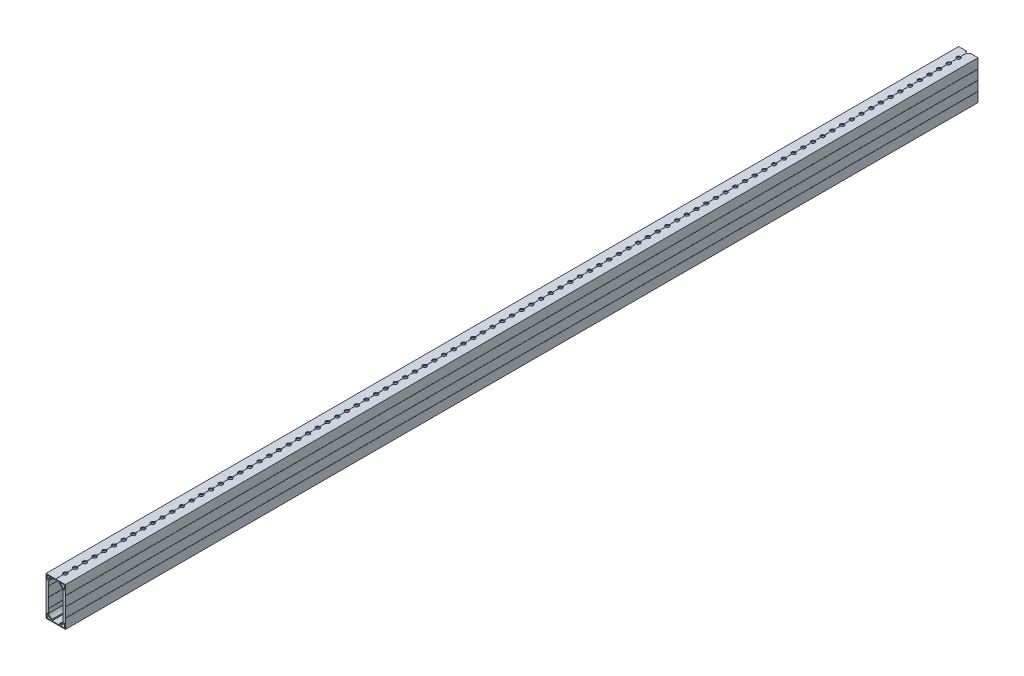
SolidWorks part; units mm, degrees
material "6061 Alloy"
ref_plane "Front Plane" through (0, 0, 0) normal (0, 0, 1) x (1, 0, 0)
ref_plane "Top Plane" through (0, 0, 0) normal (0, 1, 0) x (1, 0, 0)
ref_plane "Right Plane" through (0, 0, 0) normal (1, 0, 0) x (0, 0, -1)
other "Configuration Table"
ref_plane "Plane1" through (-12.7, 0, 0) normal (-1, 0, 0) x (0, -1, 0)
sketch "Sketch1" plane through (-12.7, 0, 0) normal (-1, 0, 0) x (0, -1, 0)
  line L0 (-25.4, -596.9) -> (25.4, -596.9)
  line L1 (25.4, -596.9) -> (25.4, 596.9)
  line L2 (25.4, 596.9) -> (-25.4, 596.9)
  line L3 (-25.4, 596.9) -> (-25.4, -596.9)
  line L4 (-25.4, -596.9) -> (25.4, 596.9) construction
  point P6 (0, 0)
  dimension "D1" = 50.8
  dimension "D2" = 1193.8
extrude "Boss-Extrude1" add sketch "Sketch1" against normal blind 25.4
sketch "Sketch2" plane through (0, 0, -596.9) normal (0, 0, -1) x (-1, 0, 0)
  line L0 (-12.7, -12.573) -> (-12.7, -12.827)
  line L1 (-12.7, -12.827) -> (-12.573, -12.7)
  line L2 (-12.573, -12.7) -> (-12.7, -12.573)
  line L5 (-0.127, 0) -> (0.127, 0)
  line L6 (0.127, 0) -> (0, 0.127)
  line L7 (0, 0.127) -> (-0.127, 0)
  line L8 (-12.7, -25.4) -> (12.7, -25.4) construction
  line L9 (-12.7, 25.4) -> (-12.7, -25.4) construction
  line L10 (12.7, -12.827) -> (12.7, -12.573)
  line L11 (12.7, -12.573) -> (12.573, -12.7)
  line L12 (12.573, -12.7) -> (12.7, -12.827)
  line L13 (12.7, 25.4) -> (12.7, -25.4) construction
  line L17 (-12.7, 0.127) -> (-12.7, -0.127)
  line L18 (-12.7, -0.127) -> (-12.573, 0)
  line L19 (-12.573, 0) -> (-12.7, 0.127)
  line L20 (-12.7, 12.827) -> (-12.7, 12.573)
  line L21 (-12.7, 12.573) -> (-12.573, 12.7)
  line L22 (-12.573, 12.7) -> (-12.7, 12.827)
  line L23 (12.7, -0.127) -> (12.7, 0.127)
  line L24 (12.7, 0.127) -> (12.573, 0)
  line L25 (12.573, 0) -> (12.7, -0.127)
  line L26 (12.7, 12.573) -> (12.7, 12.827)
  line L27 (12.7, 12.827) -> (12.573, 12.7)
  line L28 (12.573, 12.7) -> (12.7, 12.573)
  line L29 (-0.127, 25.4) -> (0.127, 25.4)
  line L30 (0.127, 25.4) -> (0, 25.273)
  line L31 (0, 25.273) -> (-0.127, 25.4)
  line L32 (-12.7, 25.4) -> (12.7, 25.4) construction
  point P3 (-12.7, -12.7)
  point P10 (0, 0)
  point P31 (-12.7, 0)
  point P36 (-12.7, 12.7)
  dimension "D1" = 0.254
  dimension "D2" = 12.7
  dimension "D3" = 25.4
  dimension "D4" = 38.1
  dimension "D6" = 0.127
  dimension "D7" = 0.254
extrude "Cut-Extrude1" cut sketch "Sketch2" against normal through all
sketch "Sketch10" plane through (0, 0, 596.9) normal (0, 0, 1) x (1, 0, 0)
  line L0 (-11.684, 24.384) -> (-11.684, 19.2971)
  line L1 (-6.5971, 24.384) -> (-11.684, 24.384)
  line L2 (-0.127, 25.4) -> (-12.7, 25.4) construction
  line L3 (-12.7, 0.127) -> (-12.7, 0)
  line L5 (-12.7, 12.827) -> (-12.573, 12.7)
  line L6 (-12.7, 12.827) -> (-12.7, 12.573)
  line L10 (0.127, 25.4) -> (0, 25.273)
  line L11 (0, 25.273) -> (-0.127, 25.4)
  line L12 (-0.127, 25.4) -> (0.127, 25.4)
  line L13 (-12.573, 12.7) -> (-12.7, 12.573)
  line L18 (-12.7, -25.4) -> (-12.7, -12.827) construction
  line L19 (12.7, -25.4) -> (-12.7, -25.4) construction
  line L43 (-12.7, 0) -> (-12.573, 0)
  line L55 (0, 24.384) -> (-4.8895, 24.384)
  line L56 (-4.8895, 24.384) -> (-4.8895, 22.679)
  line L57 (-9.525, 18.4238) -> (-9.525, 12.827)
  line L58 (-9.525, 12.827) -> (-9.652, 12.7)
  line L59 (-9.652, 12.7) -> (-9.525, 12.573)
  line L60 (-9.525, 12.573) -> (-9.525, 0.127)
  line L61 (-9.525, 0.127) -> (-9.652, 0)
  line L70 (12.7, 25.4) -> (0.127, 25.4) construction
  line L71 (-12.573, 0) -> (-12.7, 0.127)
  line L72 (-12.7, 0.127) -> (-12.7, 12.573) construction
  line L73 (-9.652, 0) -> (0, 0)
  line L74 (0, 0) -> (0, 24.384)
  arc A0 (-11.684, 19.2971) -> (-10.3994, 18.9412) centre (-10.9924, 19.2971) ccw
  arc A1 (-10.3994, 18.9412) -> (-6.2412, 23.0994) centre (0, 12.7) cw
  arc A2 (-6.2412, 23.0994) -> (-6.5971, 24.384) centre (-6.5971, 23.6924) ccw
  arc A8 (-4.8895, 22.679) -> (-9.525, 18.4238) centre (0, 12.7) ccw
  dimension "D1" = 0.6916
  dimension "D2" = 12.1285
  dimension "D3" = 45
  dimension "D11" = 11.1125
  dimension "D12" = 1.016
  dimension "D4" = 1.016
  dimension "D5" = 2.3006
  dimension "D6" = 0.127
  dimension "D7" = 25.4
  dimension "D8" = 1.016
  dimension "D9" = 45
  dimension "D10" = 3.175
  dimension "D13" = 4.8895
extrude "Cut-Extrude9" cut sketch "Sketch10" against normal through all
mirror "Mirror1" about plane through (0, 0, 0) normal (0, 1, 0) of "Cut-Extrude9" second plane through (0, 0, 0) second plane normal (1, 0, 0)
sketch "Sketch18" plane through (0, 25.4, 0) normal (0, 1, 0) x (1, 0, 0)
  line L0 (0, -596.9) -> (0, 596.9) construction
  line L1 (12.7, -596.9) -> (0.127, -596.9) construction
  circle A0 centre (0, -584.2) radius 2.54
  dimension "D1" = 5.08
  dimension "D2" = 12.7
extrude "Cut-Extrude12" cut sketch "Sketch18" against normal through all
pattern_linear "LPattern1" count 94 spacing 12.7 along (0, 0, -1) of "Cut-Extrude12"
fillet "Fillet1" radius 0.127 12 edges at (-4.8895, 22.679, 0) (-4.8895, 24.384, 0) (-9.525, 18.4238, 0) (4.8895, 24.384, 0) (4.8895, 22.679, 0) (9.525, 18.4238, 0) (-4.8895, -24.384, 0) (-4.8895, -22.679, 0) (-9.525, -18.4238, 0) (4.8895, -22.679, 0) (4.8895, -24.384, 0) (9.525, -18.4238, 0)
equation "\"Length\" = 47"
equation "\"D2@Sketch1\"=\"Length\""
